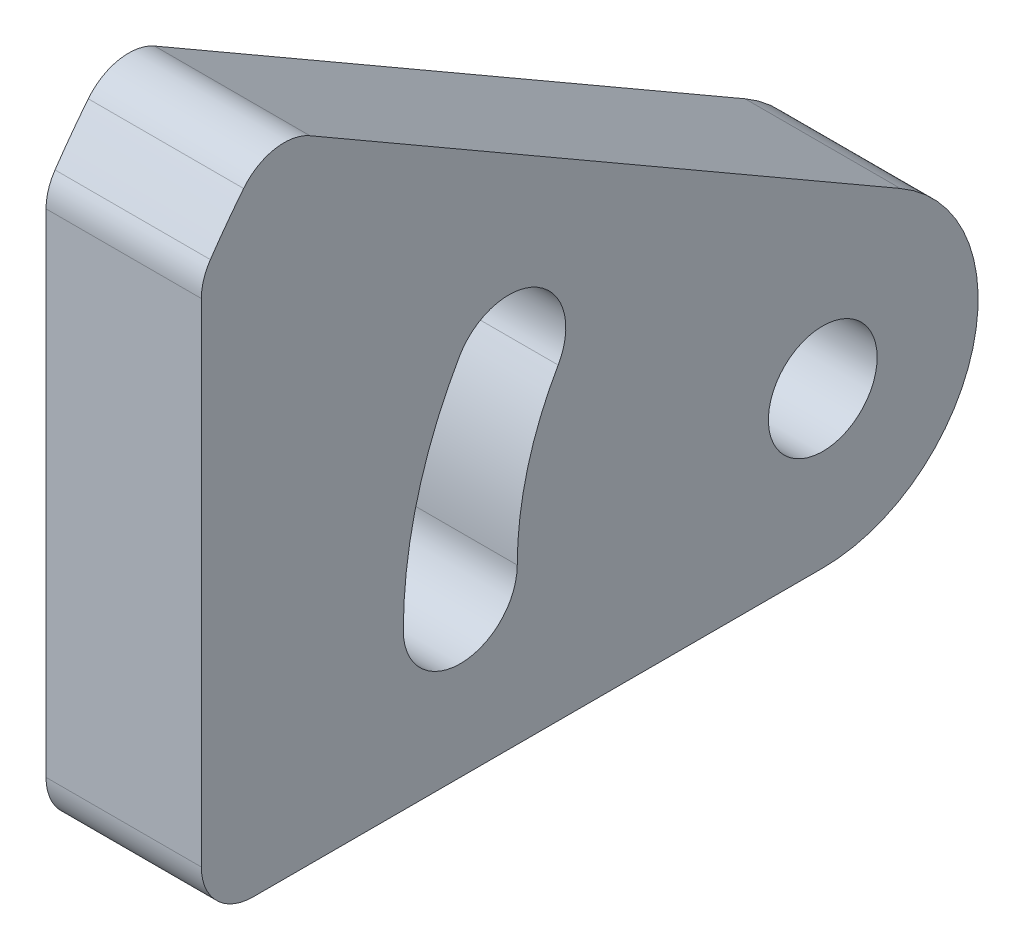
SolidWorks part; units mm, degrees
ref_plane "前视基准面" through (0, 0, 0) normal (0, 0, 1) x (1, 0, 0)
ref_plane "上视基准面" through (0, 0, 0) normal (0, 1, 0) x (1, 0, 0)
ref_plane "右视基准面" through (0, 0, 0) normal (1, 0, 0) x (0, 0, -1)
sketch "草图8" plane through (0, 0, 0) normal (1, 0, 0) x (0, 0, -1)
  line L0 (1.5, 2.5981) -> (-10.6244, 9.5981)
  line L1 (0, -3) -> (-14, -3)
  line L2 (-14, 3) -> (0.8038, 3) construction
  circle A0 centre (0, 0) radius 1.05
  arc A1 (0, -3) -> (1.5, 2.5981) centre (0, 0) ccw
  arc A2 (-10.6244, 9.5981) -> (-14, -3) centre (0, 0) ccw
  point P3 (0.6166, 3)
  dimension "D1" = 2.1
  dimension "D2" = 3
  dimension "D3" = 14
  dimension "D4" = 30
extrude "凸台-拉伸4" add sketch "草图8" along normal mid plane 3
sketch "草图14" plane through (1.5, 0, 0) normal (1, 0, 0) x (0, 0, -1)
  line L0 (-12, 7.8102) -> (-12, -3)
  line L3 (-12, -3) -> (-14.3178, -3)
  line L4 (-14.3178, -3) -> (-14.3178, 7.8102)
  line L5 (-14.3178, 7.8102) -> (-12, 7.8102)
  line L6 (-14, -3) -> (0, -3) construction
  circle A0 centre (0, 0) radius 1.05 construction
  arc A1 (-10.6244, 9.5981) -> (-14, -3) centre (0, 0) ccw construction
  arc A2 (-10.6244, 9.5981) -> (-14, -3) centre (0, 0) ccw construction
  point P4 (-12, 5.831)
  point P6 (-12, -4.1524)
  point P7 (-12, -3)
  point P14 (-13.3417, 0)
  dimension "D1" = 12
extrude "切除-拉伸3" cut sketch "草图14" against normal through all
sketch "草图17" plane through (1.5, 0, 0) normal (1, 0, 0) x (0, 0, -1)
  line L0 (-7, 0) -> (0, 0) construction
  line L1 (0, 0) -> (-6.0622, 3.5) construction
  line L2 (1.5, 2.5981) -> (-10.6244, 9.5981) construction
  arc A2 (-7, 0) -> (-6.0622, 3.5) centre (0, 0) cw construction
  arc A3 (-7.0148, 4.05) -> (-8.1, 0) centre (0, 0) ccw
  arc A4 (-5.1095, 2.95) -> (-5.9, 0) centre (0, 0) ccw
  arc A5 (-5.1095, 2.95) -> (-7.0148, 4.05) centre (-6.0622, 3.5) ccw
  arc A6 (-8.1, 0) -> (-5.9, 0) centre (-7, 0) ccw
  point P3 (-6.7615, 1.8117)
  point P15 (-7, 0)
  dimension "D1" = 1.1
  dimension "D2" = 7
extrude "切除-拉伸5" cut sketch "草图17" against normal through all
fillet "圆角3" radius 1 3 edges at (0, 9.5981, 10.6244) (0, 7.8102, 12) (0, -3, 12)
